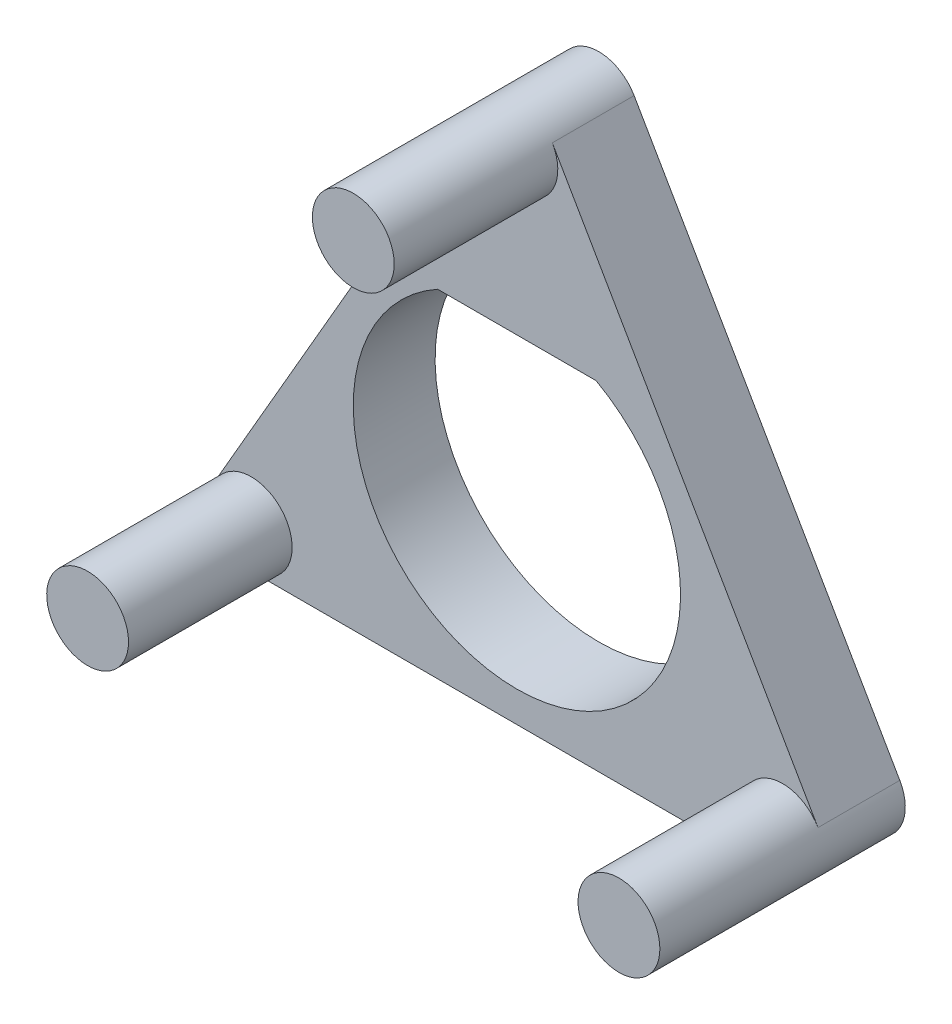
SolidWorks part; units mm, degrees
ref_plane "前视基准面" through (0, 0, 0) normal (0, 0, 1) x (1, 0, 0)
ref_plane "上视基准面" through (0, 0, 0) normal (0, 1, 0) x (1, 0, 0)
ref_plane "右视基准面" through (0, 0, 0) normal (1, 0, 0) x (0, 0, -1)
sketch "草图1" plane through (0, 0, 0) normal (0, 0, 1) x (1, 0, 0)
  line L0 (-7.3612, 1.5) -> (-0.866, 12.75)
  line L1 (0.866, 12.75) -> (7.3612, 1.5)
  line L2 (-6.4952, 0) -> (6.4952, 0)
  line L3 (0, 12.25) -> (0, 0) construction
  arc A0 (7.3612, 1.5) -> (6.4952, 0) centre (6.4952, 1) cw
  arc A1 (-6.4952, 0) -> (-7.3612, 1.5) centre (-6.4952, 1) cw
  arc A2 (0.866, 12.75) -> (-0.866, 12.75) centre (0, 12.25) ccw
  dimension "D1" = 1
extrude "凸台-拉伸1" add sketch "草图1" along normal blind 2
sketch "草图2" plane through (0, 0, 2) normal (0, 0, 1) x (1, 0, 0)
  circle A0 centre (0, 12.25) radius 1
  circle A1 centre (6.4952, 1) radius 1
  circle A2 centre (-6.4952, 1) radius 1
extrude "凸台-拉伸2" add sketch "草图2" along normal blind 4
sketch "草图3" plane through (0, 0, 2) normal (0, 0, 1) x (1, 0, 0)
  line L0 (0, 12.25) -> (-6.4952, 1) construction
  line L1 (-6.4952, 1) -> (6.4952, 1) construction
  line L2 (6.4952, 1) -> (0, 12.25) construction
  line L3 (0, 12.25) -> (0, 4.75) construction
  line L4 (0, 4.75) -> (-3.2476, 6.625) construction
  line L5 (-1.9365, 8.25) -> (1.9365, 8.25)
  arc A0 (-1.9365, 8.25) -> (1.9365, 8.25) centre (0, 4.75) ccw
  dimension "D1" = 8
  dimension "D2" = 3.5
extrude "切除-拉伸4" cut sketch "草图3" against normal blind 5 contours L5 A0
sketch "草图7" plane through (0, 0, 0) normal (0, 0, -1) x (-1, 0, 0)
  line L3 (-6.4952, 0) -> (6.4952, 0)
  line L4 (7.3612, 1.5) -> (0.866, 12.75)
  line L5 (-0.866, 12.75) -> (-7.3612, 1.5)
  line L6 (-6.4952, 0) -> (6.4952, 0)
  line L7 (7.3612, 1.5) -> (0.866, 12.75)
  line L8 (-0.866, 12.75) -> (-7.3612, 1.5)
  arc A3 (-7.3612, 1.5) -> (-6.4952, 0) centre (-6.4952, 1) ccw
  arc A4 (6.4952, 0) -> (7.3612, 1.5) centre (6.4952, 1) ccw
  arc A5 (0.866, 12.75) -> (-0.866, 12.75) centre (0, 12.25) ccw
  arc A6 (-7.3612, 1.5) -> (-6.4952, 0) centre (-6.4952, 1) ccw
  arc A7 (6.4952, 0) -> (7.3612, 1.5) centre (6.4952, 1) ccw
  arc A8 (0.866, 12.75) -> (-0.866, 12.75) centre (0, 12.25) ccw
  dimension "D1" = 0
